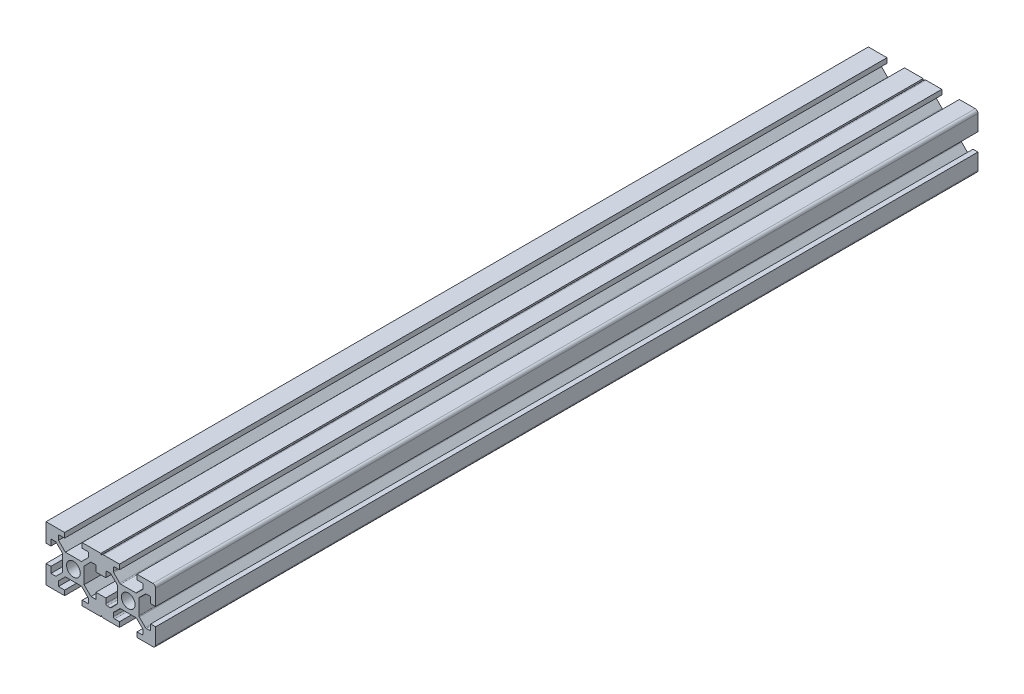
SolidWorks part; units mm, degrees
material "1060 Alloy"
ref_plane "Front Plane" through (0, 0, 0) normal (0, 0, 1) x (1, 0, 0)
ref_plane "Top Plane" through (0, 0, 0) normal (0, 1, 0) x (1, 0, 0)
ref_plane "Right Plane" through (0, 0, 0) normal (1, 0, 0) x (0, 0, -1)
sketch "Sketch1" plane through (0, 0, 0) normal (0, 0, 1) x (1, 0, 0)
  line L0 (20, 0) -> (-8.059, 28.059) construction
  line L1 (0, 0) -> (6.8, 0)
  line L2 (0, 0) -> (0, 6.8)
  line L3 (0, 20) -> (6.8, 20)
  line L4 (20, 0) -> (20, 6.8)
  line L5 (6.8, 20) -> (6.8, 18.2)
  line L6 (20, 20) -> (8.2322, 8.2322) construction
  line L7 (12.95, 6.1) -> (7.05, 6.1)
  line L8 (13.9, 7.05) -> (13.9, 12.95)
  line L9 (12.95, 13.9) -> (7.05, 13.9)
  line L10 (6.1, 7.05) -> (6.1, 12.95)
  line L11 (13.9, 6.1) -> (6.1, 13.9) construction
  line L12 (13.9, 13.9) -> (6.1, 6.1) construction
  line L13 (4.55, 16.4) -> (7.05, 13.9)
  line L14 (13.2, 18.2) -> (13.2, 20)
  line L15 (1.8, 6.8) -> (0, 6.8)
  line L16 (0, 13.2) -> (0, 20)
  line L17 (0, 13.2) -> (1.8, 13.2)
  line L18 (10, 10) -> (10, 13.9) construction
  line L19 (16.4, 4.55) -> (13.9, 7.05)
  line L20 (4.55, 16.4) -> (4.55, 18.2)
  line L21 (4.55, 18.2) -> (6.8, 18.2)
  line L22 (13.2, 18.2) -> (15.45, 18.2)
  line L23 (15.45, 18.2) -> (15.45, 16.4)
  line L24 (15.45, 16.4) -> (12.95, 13.9)
  line L25 (16.4, 4.55) -> (18.2, 4.55)
  line L26 (18.2, 4.55) -> (18.2, 6.8)
  line L27 (20, 6.8) -> (18.2, 6.8)
  line L28 (18.2, 13.2) -> (20, 13.2)
  line L29 (18.2, 13.2) -> (18.2, 15.45)
  line L30 (18.2, 15.45) -> (16.4, 15.45)
  line L31 (16.4, 15.45) -> (13.9, 12.95)
  line L32 (1.8, 4.55) -> (3.6, 4.55)
  line L33 (3.6, 15.45) -> (6.1, 12.95)
  line L34 (3.6, 15.45) -> (1.8, 15.45)
  line L35 (1.8, 15.45) -> (1.8, 13.2)
  line L36 (0, 13.2) -> (1.8, 13.2)
  line L37 (1.8, 6.8) -> (0, 6.8)
  line L38 (3.6, 4.55) -> (6.1, 7.05)
  line L39 (1.8, 6.8) -> (1.8, 4.55)
  line L40 (15.45, 3.6) -> (12.95, 6.1)
  line L41 (4.55, 3.6) -> (7.05, 6.1)
  line L42 (4.55, 1.8) -> (4.55, 3.6)
  line L43 (6.8, 1.8) -> (4.55, 1.8)
  line L44 (6.8, 1.8) -> (6.8, 0)
  line L45 (15.45, 3.6) -> (15.45, 1.8)
  line L46 (15.45, 1.8) -> (13.2, 1.8)
  line L47 (13.2, 0) -> (13.2, 1.8)
  line L48 (13.2, 20) -> (20, 20)
  line L49 (20, 13.2) -> (20, 20)
  line L50 (13.2, 0) -> (20, 0)
  line L51 (6.1, 6.1) -> (-5.5045, -5.5045) construction
  circle A0 centre (10, 10) radius 2.5
  point P25 (10, 16.4)
  point P39 (13.2, 19.1)
  point P46 (0.9, 6.8)
  dimension "D3" = 5
  dimension "D2" = 20
  dimension "D4" = 7.8
  dimension "D5" = 7.8
  dimension "D6" = 6.8
  dimension "D7" = 6.8
  dimension "D8" = 1.8
  dimension "D9" = 10.9
  dimension "D10" = 1.8
  dimension "D11" = 10.9
  dimension "D12" = 20
extrude "Boss-Extrude1" add sketch "Sketch1" along normal blind 300 contours L47 L50 L4 L27 L26 L25 L19 L8 L31 L30 L29 L28 L49 L48 L14 L22 L23 L24 L9 L13 L20 L21 L5 L3 L16 L17 L35 L34 L33 L10 L38 L32 L39 L15 L2 L1 L44 L43 L42 L41 L7 L40 L45 L46 A0
fillet "Fillet1" radius 1 4 edges at (20, 20, 150) (20, 0, 150) (0, 0, 150) (0, 20, 150)
fillet "Fillet2" radius 0.5 6 edges at (4.55, 18.2, 150) (4.55, 16.4, 150) (7.05, 13.9, 150) (15.45, 18.2, 150) (15.45, 16.4, 150) (12.95, 13.9, 150)
fillet "Fillet3" radius 0.5 6 edges at (18.2, 15.45, 150) (16.4, 15.45, 150) (13.9, 12.95, 150) (18.2, 4.55, 150) (13.9, 7.05, 150) (16.4, 4.55, 150)
fillet "Fillet4" radius 0.5 6 edges at (1.8, 15.45, 150) (3.6, 15.45, 150) (6.1, 12.95, 150) (3.6, 4.55, 150) (1.8, 4.55, 150) (6.1, 7.05, 150)
fillet "Fillet5" radius 0.5 6 edges at (7.05, 6.1, 150) (4.55, 3.6, 150) (4.55, 1.8, 150) (15.45, 1.8, 150) (15.45, 3.6, 150) (12.95, 6.1, 150)
mirror "Mirror1" about plane through (0, 0, 0) normal (1, 0, 0) of "Boss-Extrude1"
